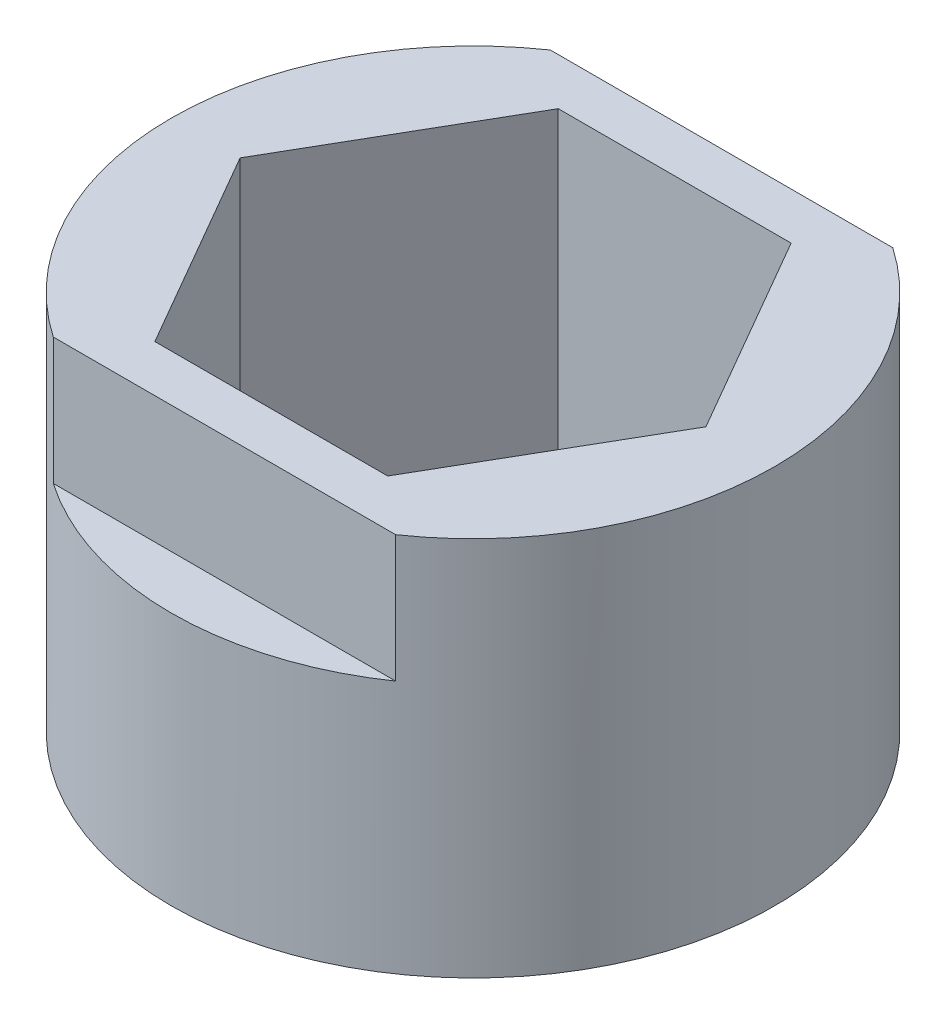
SolidWorks part; units mm, degrees
material "Polyester Resin"
ref_plane "Front Plane" through (0, 0, 0) normal (0, 0, 1) x (1, 0, 0)
ref_plane "Top Plane" through (0, 0, 0) normal (0, 1, 0) x (1, 0, 0)
ref_plane "Right Plane" through (0, 0, 0) normal (1, 0, 0) x (0, 0, -1)
sketch "Sketch1" plane through (0, 0, 0) normal (0, 1, 0) x (1, 0, 0)
  line L1 (-2.9156, 5.05) -> (-5.8312, 0)
  line L2 (-5.8312, 0) -> (-2.9156, -5.05)
  line L3 (-2.9156, -5.05) -> (2.9156, -5.05)
  line L4 (2.9156, -5.05) -> (5.8312, 0)
  line L5 (5.8312, 0) -> (2.9156, 5.05)
  line L6 (2.9156, 5.05) -> (-2.9156, 5.05)
  circle A0 centre (0, 0) radius 5.05 construction
  circle A1 centre (0, 0) radius 7.5565
  dimension "D2" = 15.113
  dimension "D1" = 10.1
extrude "Boss-Extrude1" add sketch "Sketch1" along normal blind 8.89
sketch "Sketch2" plane through (0, 0, 0) normal (0, -1, 0) x (1, 0, 0)
  circle A0 centre (0, 0) radius 7.5565
  circle A1 centre (0, 0) radius 3.3
  dimension "D1" = 6.6
extrude "Boss-Extrude2" add sketch "Sketch2" along normal blind 0.635
sketch "Sketch3" plane through (0, 0, 0) normal (1, 0, 0) x (0, 0, -1)
  line L0 (-6.223, 9.525) -> (-6.223, 5.715)
  line L1 (6.223, 9.525) -> (6.223, 5.715)
  line L2 (-7.5565, -0.635) -> (7.5565, -0.635) construction
  line L3 (-6.223, 9.525) -> (-8.202, 9.525)
  line L4 (-8.202, 9.525) -> (-8.202, 5.715)
  line L5 (-8.202, 5.715) -> (-6.223, 5.715)
  line L6 (6.223, 9.525) -> (8.4791, 9.525)
  line L7 (8.4791, 9.525) -> (8.4791, 5.715)
  line L8 (8.4791, 5.715) -> (6.223, 5.715)
  dimension "D1" = 12.446
  dimension "D2" = 6.223
  dimension "D3" = 3.81
  dimension "D4" = 3.81
  dimension "D5" = 6.35
  dimension "D6" = 6.35
extrude "Cut-Extrude1" cut sketch "Sketch3" against normal through all and the other way through all
equation "\"AB_Central_Bushing_Length\" = .75in"
equation "\"Solid_Length\"= .025in"
equation "\"Hex_Length\"= 0.35"
equation "\"D1@Boss-Extrude1\"= \"Hex_Length\""
equation "\"D1@Boss-Extrude2\"=\"Solid_Length\""
equation "\"Cutout_Angle\" = 80"
